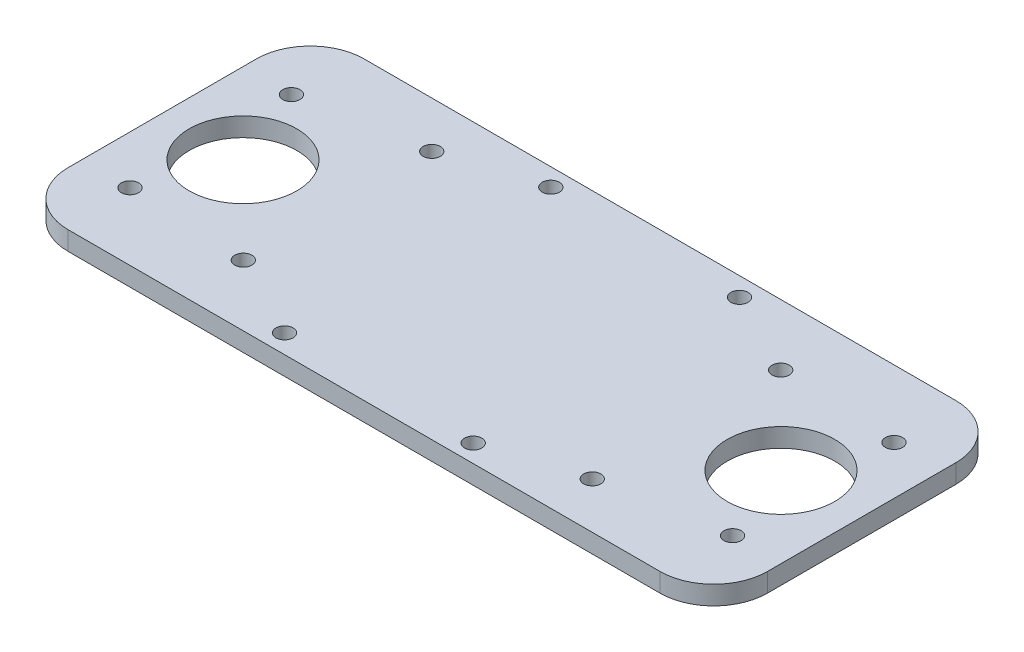
SolidWorks part; units mm, degrees
ref_plane "Front Plane" through (0, 0, 0) normal (0, 0, 1) x (1, 0, 0)
ref_plane "Top Plane" through (0, 0, 0) normal (0, 1, 0) x (1, 0, 0)
ref_plane "Right Plane" through (0, 0, 0) normal (1, 0, 0) x (0, 0, -1)
sketch "Sketch1" plane through (0, 0, 0) normal (0, 1, 0) x (1, 0, 0)
  line L0 (65, 20.185) -> (65, -60.6934) construction
  line L1 (0, 0) -> (130, 0)
  line L2 (0, 0) -> (0, -55)
  line L3 (0, -55) -> (130, -55)
  line L4 (130, 0) -> (130, -55)
  line L5 (-10.4412, -27.5) -> (139.8504, -27.5) construction
  circle A0 centre (9, -12.5) radius 1.6
  circle A1 centre (9, -42.5) radius 1.6
  circle A4 centre (121, -42.5) radius 1.6
  circle A7 centre (121, -12.5) radius 1.6
  circle A12 centre (15, -27.5) radius 10
  circle A13 centre (115, -27.5) radius 10
  circle A18 centre (48.0169, -3.3) radius 1.6
  circle A19 centre (46.7169, -51.5) radius 1.6
  circle A20 centre (98.8169, -46.4) radius 1.6
  circle A21 centre (98.8169, -11.3789) radius 1.6
  circle A22 centre (31.1831, -43.6211) radius 1.6
  circle A23 centre (31.1831, -8.6) radius 1.6
  circle A24 centre (83.2831, -3.5) radius 1.6
  circle A25 centre (81.9831, -51.7) radius 1.6
  point P27 (65, -27.5)
  point P41 (65, -27.5)
  dimension "D3" = 3.2
  dimension "D4" = 3.2
  dimension "D5" = 48.2
  dimension "D6" = 1.3
  dimension "D13" = 3.5
  dimension "D14" = 3.2
  dimension "D15" = 3.2
  dimension "D16" = 3.2
  dimension "D25" = 20
  dimension "D27" = 20
  dimension "D8" = 50.8
  dimension "D9" = 0
  dimension "D17" = 3.2
  dimension "D1" = 130
  dimension "D2" = 55
  dimension "D7" = 30
  dimension "D10" = 5.1
  dimension "D11" = 65
  dimension "D12" = 9
  dimension "D18" = 2
  dimension "D26" = 15
  dimension "D28" = 15
extrude "Boss-Extrude3" add sketch "Sketch1" along normal blind 3.5
fillet "Fillet3" radius 10 4 edges at (0, 1.75, 0) (0, 1.75, 55) (130, 1.75, 55) (130, 1.75, 0)
